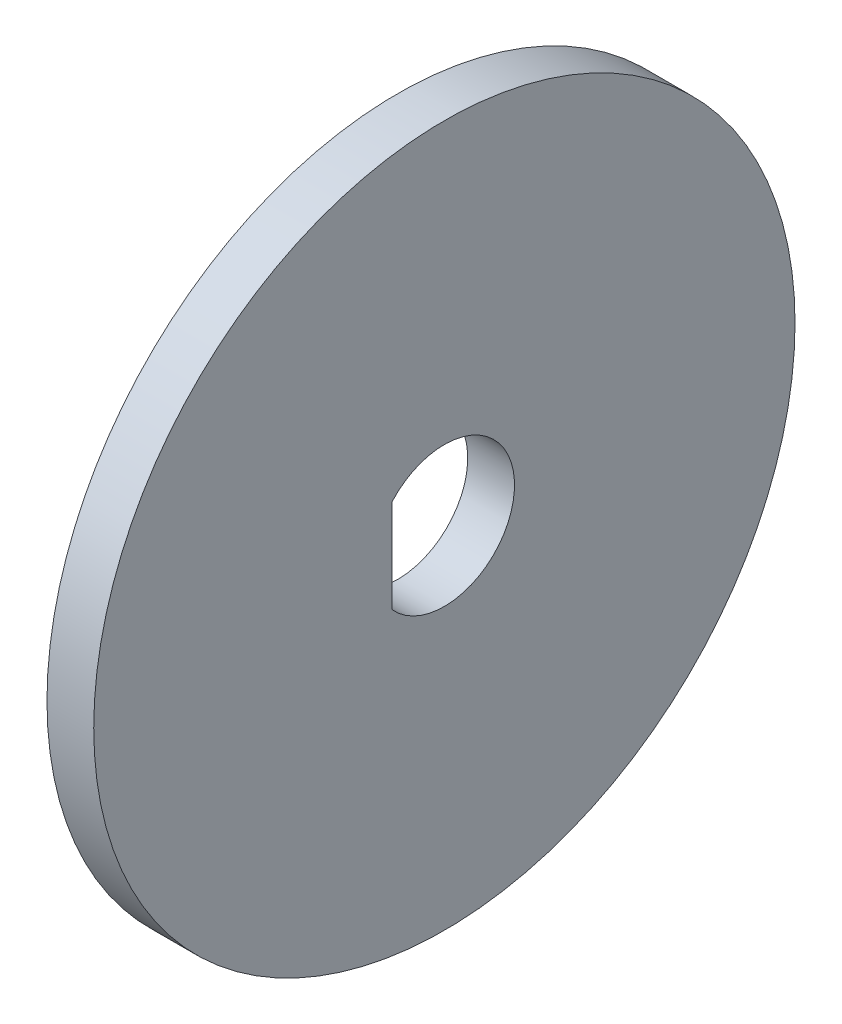
SolidWorks part; units mm, degrees
material "Pine"
ref_plane "Front Plane" through (0, 0, 0) normal (0, 0, 1) x (1, 0, 0)
ref_plane "Top Plane" through (0, 0, 0) normal (0, 1, 0) x (1, 0, 0)
ref_plane "Right Plane" through (0, 0, 0) normal (1, 0, 0) x (0, 0, -1)
sketch "Sketch1" plane through (0, 0, 0) normal (1, 0, 0) x (0, 0, -1)
  circle A0 centre (0, 0) radius 15
  dimension "D1" = 30
extrude "Boss-Extrude1" add sketch "Sketch1" along normal blind 2
sketch "Sketch2" plane through (2, 0, 0) normal (1, 0, 0) x (0, 0, -1)
  line L0 (-2.2361, 2) -> (-2.2361, -2)
  arc A0 (-2.2361, -2) -> (-2.2361, 2) centre (0, 0) ccw
  dimension "D1" = 6
  dimension "D2" = 4
extrude "Cut-Extrude1" cut sketch "Sketch2" against normal through all
